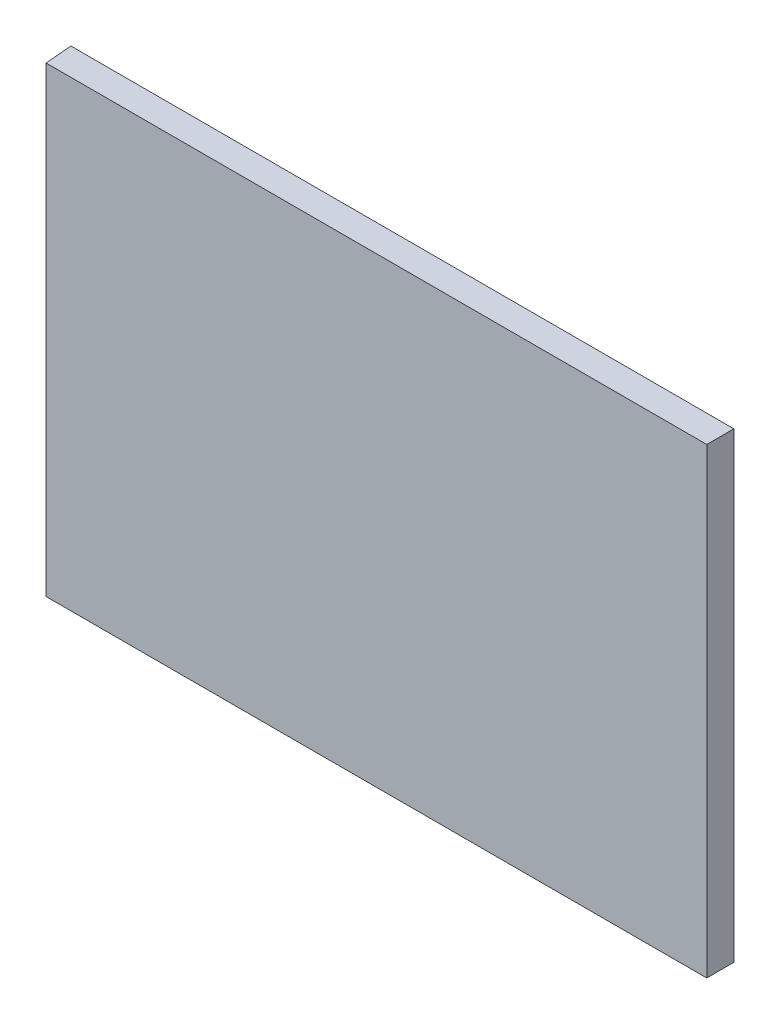
SolidWorks part; units mm, degrees
ref_plane "前视基准面" through (0, 0, 0) normal (0, 0, 1) x (1, 0, 0)
ref_plane "上视基准面" through (0, 0, 0) normal (0, 1, 0) x (1, 0, 0)
ref_plane "右视基准面" through (0, 0, 0) normal (1, 0, 0) x (0, 0, -1)
other "Configuration Table"
sketch "草图4" plane through (0, 0, 0) normal (0, 0, 1) x (1, 0, 0)
  line L0 (-11.0381, 9) -> (14.9119, 9)
  line L1 (-11.0381, 9) -> (-11.0381, -12.04)
  line L2 (-11.0381, -12.04) -> (14.9119, -12.04)
  line L3 (14.9119, 9) -> (14.9119, -12.04)
  dimension "D1" = 21.04
  dimension "D2" = 25.95
extrude "凸台-拉伸1" add sketch "草图4" along normal blind 1
sketch "草图6" plane through (0, 9, 0) normal (0, 1, 0) x (1, 0, 0)
  line L0 (-11.0381, 0) -> (-11.0381, -1)
  line L1 (-11.0381, -1) -> (-10.9506, -1)
  line L2 (14.9119, -1) -> (-11.0381, -1) construction
  line L3 (-10.9506, -1) -> (-11.0381, 0)
  dimension "D1" = 5
extrude "切除-拉伸1" cut sketch "草图6" against normal through all
sketch "草图7" plane through (0, 9, 0) normal (0, 1, 0) x (1, 0, 0)
  line L0 (14.9119, -1) -> (14.8944, 0)
  line L1 (14.9119, 0) -> (-11.0381, 0) construction
  line L2 (14.8944, 0) -> (14.9119, 0)
  line L3 (14.9119, 0) -> (14.9119, -1)
  dimension "D1" = 1
extrude "切除-拉伸2" cut sketch "草图7" against normal through all
sketch "草图11" plane through (0, 0, 0) normal (1, 0, 0) x (0, 0, -1)
  line L0 (-1, -12.04) -> (0, -12.04)
  line L1 (0, -12.04) -> (0, -12.0225)
  line L2 (0, -12.04) -> (0, 9) construction
  line L3 (0, -12.0225) -> (-1, -12.04)
  dimension "D1" = 1
extrude "切除-拉伸4" cut sketch "草图11" against normal through all and the other way through all
sketch "草图12" plane through (0, 0, 0) normal (1, 0, 0) x (0, 0, -1)
  line L3 (-1, 9) -> (0, 9)
  line L4 (-1, 9) -> (0, 8.9825)
  line L5 (0, -12.0225) -> (0, 9) construction
  line L6 (0, 8.9825) -> (0, 9)
  dimension "D1" = 1
extrude "切除-拉伸5" cut sketch "草图12" against normal through all and the other way through all
sketch "草图13" plane through (0, 0, 1) normal (0, 0, 1) x (1, 0, 0)
  line L0 (-10.9506, 7) -> (13.4119, 7)
  line L1 (-10.9506, -12.04) -> (-10.9506, 9) construction
  line L2 (13.4119, 7) -> (13.4119, -10.04)
  line L3 (13.4119, -10.04) -> (-10.9506, -10.04)
  line L4 (-10.9506, -10.04) -> (-10.9506, -12.04)
  line L5 (-10.9506, -12.04) -> (14.9119, -12.04)
  line L6 (14.9119, -12.04) -> (14.9119, 9)
  line L7 (14.9119, 9) -> (-10.9506, 9)
  line L8 (-10.9506, 9) -> (-10.9506, 7)
  dimension "D1" = 2
  dimension "D2" = 2
  dimension "D3" = 1.5
extrude "切除-拉伸6" cut sketch "草图13" against normal up to surface (1 mm away) up to face at (1.9281, -1.52, 0)
sketch "草图14" plane through (-10.9506, 0, 0) normal (1, 0, 0) x (0, 0, -1)
  line L1 (-1, 9) -> (0, 9)
  line L2 (-1, 9) -> (-1, 7)
  line L3 (-1, 7) -> (0, 7)
  line L4 (0, 9) -> (0, 7)
  line L5 (-1, -10.04) -> (0, -10.04)
  line L6 (-1, -10.04) -> (-1, -12.04)
  line L7 (-1, -12.04) -> (0, -12.04)
  line L8 (0, -10.04) -> (0, -12.04)
extrude "切除-拉伸7" cut sketch "草图14" against normal blind 10
